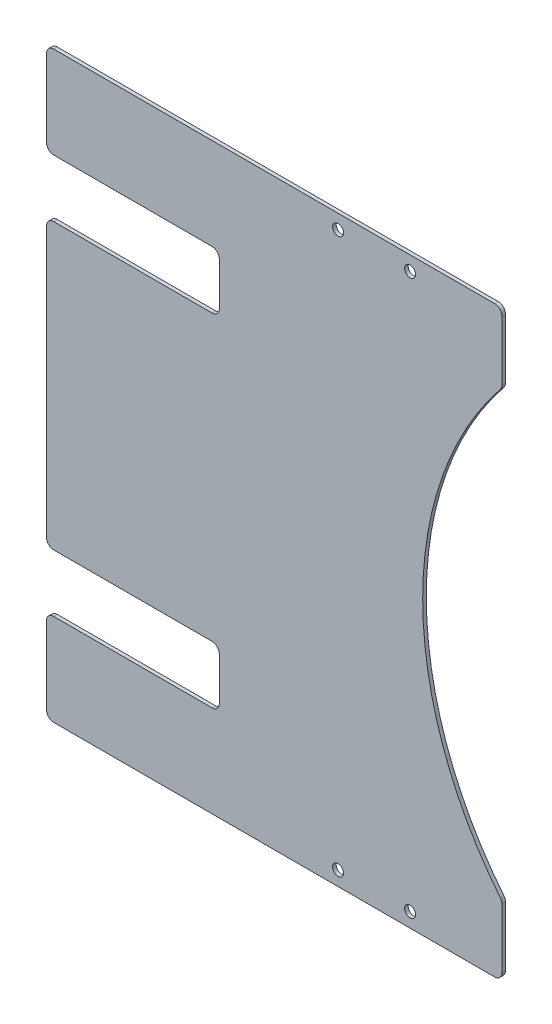
SolidWorks part; units mm, degrees
material "Thornel Mat VMA"
ref_plane "前视基准面" through (0, 0, 0) normal (0, 0, 1) x (1, 0, 0)
ref_plane "上视基准面" through (0, 0, 0) normal (0, 1, 0) x (1, 0, 0)
ref_plane "右视基准面" through (0, 0, 0) normal (1, 0, 0) x (0, 0, -1)
other "Configuration Table"
sketch "草图1" plane through (0, 0, 0) normal (0, 0, 1) x (1, 0, 0)
  line L0 (0, 0) -> (-50000, 0) construction
  line L1 (-10, -77) -> (10, -77) construction
  line L2 (-10, -77) -> (-10, 77) construction
  line L3 (-10, 77) -> (10, 77) construction
  line L4 (10, -77) -> (10, 77) construction
  line L5 (-10, -77) -> (10, 77) construction
  line L6 (-10, 77) -> (10, -77) construction
  line L8 (-45, -81) -> (35.5, -81)
  line L9 (-45, -81) -> (-45, 81)
  line L10 (-45, 81) -> (35.5, 81)
  line L11 (35.5, -81) -> (35.5, 81)
  line L12 (-45, -81) -> (35.5, 81) construction
  line L13 (-45, 81) -> (35.5, -81) construction
  circle A0 centre (-10, 77) radius 1.525
  circle A1 centre (10, 77) radius 1.525
  circle A2 centre (-10, -77) radius 1.525
  circle A3 centre (10, -77) radius 1.525
  point P0 (0, 0)
  point P12 (-4.75, 0)
  dimension "D1" = 3.05
  dimension "D2" = 20
  dimension "D3" = 154
  dimension "D4" = 4
  dimension "D5" = 35
  dimension "D6" = 45.5
extrude "凸台-拉伸1" add sketch "草图1" along normal blind 1
sketch "草图2" plane through (0, 0, 0) normal (0, 0, -1) x (-1, 0, 0)
  circle A0 centre (-111, 0) radius 97.5
  dimension "D1" = 195
extrude "切除-拉伸1" cut sketch "草图2" against normal blind 1
fillet "圆角1" radius 2 6 edges at (35.5, -81, 0.5) (-45, -81, 0.5) (35.5, 81, 0.5) (35.5, -61.6928, 0.5) (35.5, 61.6928, 0.5) (-45, 81, 0.5)
sketch "草图3" plane through (0, 0, 1) normal (0, 0, 1) x (1, 0, 0)
  line L0 (0, 0) -> (-50000, 0) construction
  line L1 (-45, 79) -> (-45, -79) construction
  line L2 (-91, 55.5) -> (-45, 55.5)
  line L3 (-91, 55.5) -> (-91, 39.5)
  line L4 (-91, 39.5) -> (-45, 39.5)
  line L5 (-45, 55.5) -> (-45, 39.5)
  line L6 (-91, -39.5) -> (-45, -39.5)
  line L7 (-91, -39.5) -> (-91, -55.5)
  line L8 (-91, -55.5) -> (-45, -55.5)
  line L9 (-45, -39.5) -> (-45, -55.5)
  line L10 (-43, -81) -> (33.5, -81) construction
  line L11 (-43, 81) -> (-91, 81)
  line L12 (-43, 81) -> (-43, -81)
  line L13 (-43, -81) -> (-91, -81)
  line L14 (-91, 81) -> (-91, -81)
  arc M18 (-43, 81) -> (-45, 79) centre (-43, 79) ccw
  line M19 (-45, 79) -> (-45, -79)
  arc M20 (-45, -79) -> (-43, -81) centre (-43, -79) ccw
  dimension "D1" = 95
  dimension "D2" = 16
  dimension "D3" = 46
extrude "凸台-拉伸2" add sketch "草图3" against normal up to surface (1 mm away) contours L11 L14 L2 M19 M18 | L0 L4 L14 M19 | L0 L14 L6 M19 | L8 L14 L13 M20 M19
fillet "圆角2" radius 2 10 edges at (-45, 39.5, 0.5) (-91, -39.5, 0.5) (-45, -39.5, 0.5) (-45, -55.5, 0.5) (-91, -55.5, 0.5) (-91, -81, 0.5) (-91, 81, 0.5) (-91, 55.5, 0.5) (-45, 55.5, 0.5) (-91, 39.5, 0.5)
sketch "草图4" plane through (0, 0, 1) normal (0, 0, 1) x (1, 0, 0)
  line L0 (-47, 55.5) -> (-43, 55.5)
  line L1 (-43, 55.5) -> (-43, 39.5)
  line L2 (-43, 39.5) -> (-47, 39.5)
  line L3 (-47, -39.5) -> (-43, -39.5)
  line L4 (-43, -39.5) -> (-43, -55.5)
  line L5 (-43, -55.5) -> (-47, -55.5)
  line L6 (-45, -41.5) -> (-45, -53.5) construction
  line L7 (-45, 53.5) -> (-45, 41.5) construction
  line L8 (-45, -41.5) -> (-45, -53.5)
  line L9 (-45, 53.5) -> (-45, 41.5)
  arc A0 (-47, -55.5) -> (-45, -53.5) centre (-47, -53.5) ccw construction
  arc A1 (-45, -41.5) -> (-47, -39.5) centre (-47, -41.5) ccw construction
  arc A2 (-47, 39.5) -> (-45, 41.5) centre (-47, 41.5) ccw construction
  arc A3 (-45, 53.5) -> (-47, 55.5) centre (-47, 53.5) ccw construction
  arc A4 (-47, -55.5) -> (-45, -53.5) centre (-47, -53.5) ccw
  arc A5 (-45, -41.5) -> (-47, -39.5) centre (-47, -41.5) ccw
  arc A6 (-47, 39.5) -> (-45, 41.5) centre (-47, 41.5) ccw
  arc A7 (-45, 53.5) -> (-47, 55.5) centre (-47, 53.5) ccw
  dimension "D1" = 2
extrude "切除-拉伸2" cut sketch "草图4" against normal blind 10
fillet "圆角3" radius 2 4 edges at (-43, -39.5, 0.5) (-43, -55.5, 0.5) (-43, 55.5, 0.5) (-43, 39.5, 0.5)
